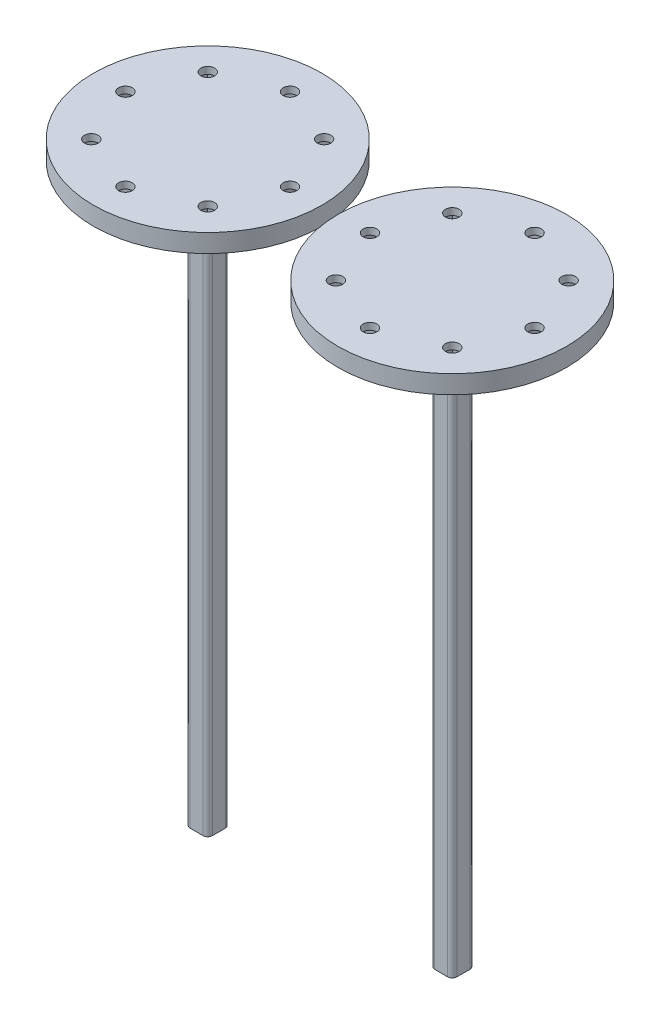
SolidWorks part; units mm, degrees
ref_plane "前视基准面" through (0, 0, 0) normal (0, 0, 1) x (1, 0, 0)
ref_plane "上视基准面" through (0, 0, 0) normal (0, 1, 0) x (1, 0, 0)
ref_plane "右视基准面" through (0, 0, 0) normal (1, 0, 0) x (0, 0, -1)
sketch "草图1" plane through (0, 0, 0) normal (0, 1, 0) x (1, 0, 0)
  circle A0 centre (0, 0) radius 20
  dimension "D1" = 40
extrude "凸台-拉伸1" add sketch "草图1" along normal blind 4
sketch "草图2" plane through (0, 0, 0) normal (0, -1, 0) x (1, 0, 0)
  circle A0 centre (0, 0) radius 7.4071
extrude "凸台-拉伸2" add sketch "草图2" along normal blind 8
sketch "草图3" plane through (0, -8, 0) normal (0, -1, 0) x (1, 0, 0)
  line L1 (-2.425, -2.425) -> (2.425, -2.425)
  line L2 (-2.425, -2.425) -> (-2.425, 2.425)
  line L3 (-2.425, 2.425) -> (2.425, 2.425)
  line L4 (2.425, -2.425) -> (2.425, 2.425)
  line L5 (-2.425, -2.425) -> (2.425, 2.425) construction
  line L6 (-2.425, 2.425) -> (2.425, -2.425) construction
  point P0 (0, 0)
  dimension "D1" = 4.85
  dimension "D2" = 4.85
extrude "凸台-拉伸3" add sketch "草图3" along normal blind 118
sketch "草图5" plane through (0, 4, 0) normal (0, 1, 0) x (1, 0, 0)
  circle A0 centre (0, 0) radius 25
  dimension "D1" = 50
extrude "凸台-拉伸4" add sketch "草图5" against normal blind 4
sketch "草图6" plane through (0, 0, 0) normal (0, -1, 0) x (1, 0, 0)
  line L3 (21.2332, 0) -> (19.6166, 2.8)
  line L4 (19.6166, 2.8) -> (16.3834, 2.8)
  line L5 (16.3834, 2.8) -> (14.7668, 0)
  line L6 (14.7668, 0) -> (16.3834, -2.8)
  line L7 (16.3834, -2.8) -> (19.6166, -2.8)
  line L8 (19.6166, -2.8) -> (21.2332, 0)
  circle A0 centre (18, 0) radius 2.8 construction
  dimension "D1" = 5.6
extrude "切除-拉伸1" cut sketch "草图6" against normal blind 2.5
sketch "草图7" plane through (0, 2.5, 0) normal (0, -1, 0) x (1, 0, 0)
  circle A0 centre (18, 0) radius 1.5
  dimension "D1" = 3
extrude "切除-拉伸2" cut sketch "草图7" against normal blind 2.5
pattern_circular "阵列(圆周)1" count 8 over 360 about axis through (0, 0, 0) along (0, 1, 0) of "切除-拉伸1", "切除-拉伸2"
fillet "圆角1" radius 1 4 edges at (2.425, -67, -2.425) (2.425, -67, 2.425) (-2.425, -67, 2.425) (-2.425, -67, -2.425)
sketch "草图9" plane through (0, 0, 0) normal (0, 1, 0) x (1, 0, 0)
  circle A0 centre (53.4876, 0) radius 25
  dimension "D1" = 50
extrude "凸台-拉伸5" add sketch "草图9" along normal blind 4 separate body
sketch "草图10" plane through (0, 0, 0) normal (0, -1, 0) x (1, 0, 0)
  circle A0 centre (53.4876, 0) radius 5.5
  dimension "D1" = 11
extrude "凸台-拉伸6" add sketch "草图10" along normal blind 8
sketch "草图11" plane through (0, -8, 0) normal (0, -1, 0) x (1, 0, 0)
  line L2 (51.0626, -2.425) -> (55.9126, -2.425)
  line L3 (51.0626, -2.425) -> (51.0626, 2.425)
  line L4 (51.0626, 2.425) -> (55.9126, 2.425)
  line L5 (55.9126, -2.425) -> (55.9126, 2.425)
  line L6 (51.0626, -2.425) -> (55.9126, 2.425) construction
  line L7 (51.0626, 2.425) -> (55.9126, -2.425) construction
  dimension "D1" = 4.85
  dimension "D2" = 4.85
extrude "凸台-拉伸7" add sketch "草图11" along normal blind 118
sketch "草图12" plane through (0, -126, 0) normal (0, -1, 0) x (1, 0, 0)
  line L3 (38.7207, 0) -> (37.1041, 2.8)
  line L4 (37.1041, 2.8) -> (33.871, 2.8)
  line L5 (33.871, 2.8) -> (32.2544, 0)
  line L6 (32.2544, 0) -> (33.871, -2.8)
  line L7 (33.871, -2.8) -> (37.1041, -2.8)
  line L8 (37.1041, -2.8) -> (38.7207, 0)
  circle A0 centre (35.4876, 0) radius 2.8 construction
  dimension "D3" = 5.6
extrude "切除-拉伸7" cut sketch "草图12" against normal blind 128.5
sketch "草图13" plane through (0, 2.5, 0) normal (0, -1, 0) x (1, 0, 0)
  circle A0 centre (35.4876, 0) radius 1.5
  dimension "D1" = 3
extrude "切除-拉伸8" cut sketch "草图13" against normal blind 128.5
pattern_circular "阵列(圆周)2" count 8 over 360 about axis through (53.4876, 0, 0) along (0, 1, 0) of "切除-拉伸8", "切除-拉伸7"
fillet "圆角2" radius 1 4 edges at (51.0626, -67, -2.425) (55.9126, -67, -2.425) (51.0626, -67, 2.425) (55.9126, -67, 2.425)
sketch "草图14" plane through (0, -8, 0) normal (0, -1, 0) x (1, 0, 0)
  circle A0 centre (0, 0) radius 5.5
  circle A1 centre (0, 0) radius 7.4071
  dimension "D1" = 11
extrude "切除-拉伸9" cut sketch "草图14" against normal blind 8
